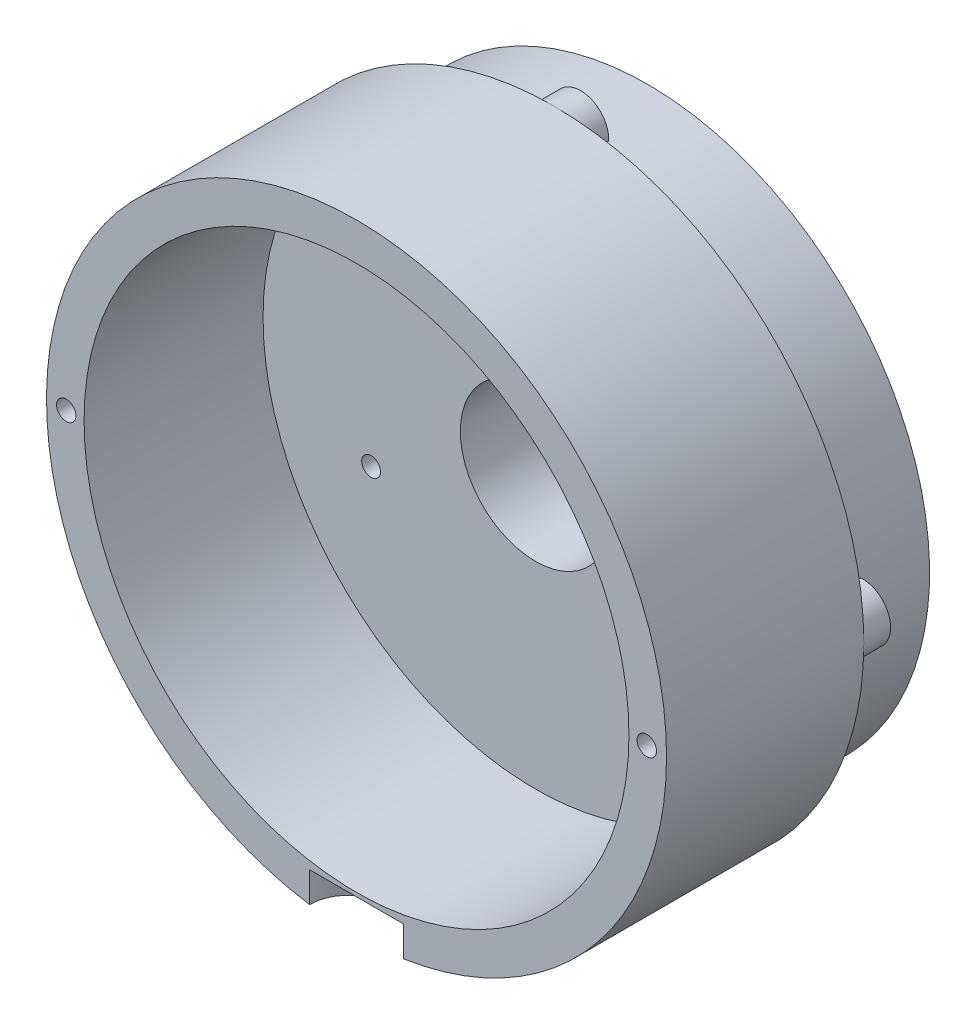
SolidWorks part; units mm, degrees
ref_plane "Front Plane" through (0, 0, 0) normal (0, 0, 1) x (1, 0, 0)
ref_plane "Top Plane" through (0, 0, 0) normal (0, 1, 0) x (1, 0, 0)
ref_plane "Right Plane" through (0, 0, 0) normal (1, 0, 0) x (0, 0, -1)
sketch "Sketch1" plane through (0, 0, 0) normal (0, 0, 1) x (1, 0, 0)
  circle A0 centre (0, 0) radius 33
  dimension "D1" = 66
extrude "Boss-Extrude1" add sketch "Sketch1" against normal blind 21
sketch "Sketch2" plane through (0, 0, 0) normal (0, 0, 1) x (1, 0, 0)
  circle A0 centre (0, 0) radius 29
  dimension "D1" = 58
extrude "Cut-Extrude1" cut sketch "Sketch2" against normal blind 19.05
sketch "Sketch3" plane through (0, 0, -21) normal (0, 0, -1) x (-1, 0, 0)
  circle A0 centre (0, 0) radius 30
  dimension "D1" = 60
extrude "Boss-Extrude2" add sketch "Sketch3" along normal blind 10
sketch "Sketch4" plane through (0, 0, -21) normal (0, 0, -1) x (-1, 0, 0)
  arc A0 (-29.85, 2.9962) -> (-29.85, -2.9962) centre (-30, 0) ccw
  circle A1 centre (0, 0) radius 30 construction
  circle A2 centre (0, 0) radius 30 construction
  arc A3 (-29.85, 2.9962) -> (-29.85, -2.9962) centre (0, 0) ccw
  arc A4 (2.9962, 29.85) -> (-2.9962, 29.85) centre (0, 30) ccw
  arc A5 (29.85, -2.9962) -> (29.85, 2.9962) centre (30, 0) ccw
  arc A6 (-2.9962, -29.85) -> (2.9962, -29.85) centre (0, -30) ccw
  arc A7 (2.9962, 29.85) -> (-2.9962, 29.85) centre (0, 0) ccw
  arc A8 (29.85, -2.9962) -> (29.85, 2.9962) centre (0, 0) ccw
  arc A9 (-2.9962, -29.85) -> (2.9962, -29.85) centre (0, 0) ccw
  point P22 (0, 0)
  dimension "D1" = 6
  dimension "D2" = 4
extrude "Boss-Extrude3" add sketch "Sketch4" along normal blind 2.85
sketch "Sketch5" plane through (0, 0, -31) normal (0, 0, -1) x (-1, 0, 0)
  line L0 (0, 0) -> (0, 30) construction
  circle A0 centre (0, 0) radius 8
  circle A1 centre (0, 15) radius 3
  circle A2 centre (0, 0) radius 30 construction
  dimension "D1" = 16
  dimension "D2" = 6
  dimension "D3" = 15
extrude "Cut-Extrude2" cut sketch "Sketch5" against normal through all contours A1 L0 | L0 A1 | A0
sketch "Sketch6" plane through (0, 0, -19.05) normal (0, 0, 1) x (1, 0, 0)
  circle A0 centre (0, 15) radius 4.1
  dimension "D1" = 8.2
extrude "Cut-Extrude3" cut sketch "Sketch6" against normal blind 3
sketch "Sketch9" plane through (0, 0, 0) normal (1, 0, 0) x (0, 0, -1)
  line L0 (31, 15) -> (19.05, 15) construction
  line L1 (31, 12) -> (31, 18) construction
  line L2 (19.05, 19.1) -> (19.05, 10.9) construction
  line L3 (22.05, 18) -> (22.05, 18.8)
  line L4 (22.05, 19.1) -> (22.05, 10.9) construction
  line L5 (22.05, 18.8) -> (31, 18)
  line L6 (31, -30) -> (31, 30) construction
  line L7 (31, 18) -> (22.05, 18)
  dimension "D1" = 0.8
revolve "Cut-Revolve1" cut sketch "Sketch9" angle 360 about L0
sketch "Sketch10" plane through (0, 0, 0) normal (0, 0, 1) x (1, 0, 0)
  line L0 (0, 0) -> (-33, 0) construction
  line L1 (0, 0) -> (0, -8) construction
  circle A0 centre (0, 0) radius 33 construction
  circle A1 centre (-30.9, 0) radius 1.0325
  circle A2 centre (0, 0) radius 8 construction
  circle A3 centre (30.9, 0) radius 1.0325
  dimension "D1" = 2.065
  dimension "D2" = 30.9
extrude "Cut-Extrude4" cut sketch "Sketch10" against normal blind 5
ref_plane "Plane1" through (0, -33, 0) normal (0, -1, 0) x (-1, 0, 0)
sketch "Sketch11" plane through (0, -33, 0) normal (0, -1, 0) x (-1, 0, 0)
  line L0 (-5, 0) -> (5, 0)
  arc A0 (5, 0) -> (-5, 0) centre (0, 0) ccw
  dimension "D1" = 10
extrude "Cut-Extrude5" cut sketch "Sketch11" against normal blind 3.6
sketch "Sketch12" plane through (0, 0, -19.05) normal (0, 0, 1) x (1, 0, 0)
  line L0 (0, 0) -> (0, -8) construction
  line L1 (0, -8) -> (17.5, -8) construction
  circle A0 centre (17.5, -8) radius 1
  circle A1 centre (-17.5, -8) radius 1
  dimension "D3" = 2
  dimension "D1" = 8
  dimension "D2" = 17.5
extrude "Cut-Extrude6" cut sketch "Sketch12" against normal blind 3
